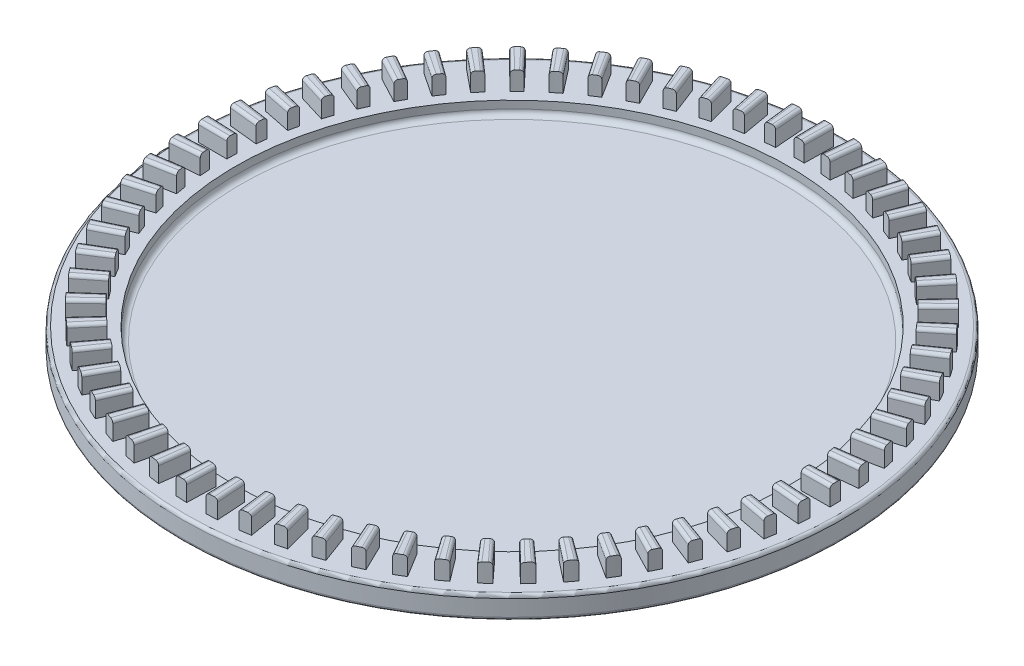
SolidWorks part; units mm, degrees
material "Copper"
ref_plane "Front Plane" through (0, 0, 0) normal (0, 0, 1) x (1, 0, 0)
ref_plane "Top Plane" through (0, 0, 0) normal (0, 1, 0) x (1, 0, 0)
ref_plane "Right Plane" through (0, 0, 0) normal (1, 0, 0) x (0, 0, -1)
sketch "Sketch3" plane through (0, 0, 0) normal (0, 0, 1) x (1, 0, 0)
  line L0 (-30.8, 1.22) -> (-26.1, 1.22)
  line L2 (-31.1, 0.92) -> (-31.1, -0.6072)
  line L3 (-25.6, 0) -> (0, 0)
  line L4 (-28.5151, -1.5) -> (0, -1.5)
  line L5 (0, -1.5) -> (0, 0)
  line L6 (-26.1, 1.22) -> (-26.1, 0.5)
  line L7 (0, 249.9038) -> (0, -246.3343) construction
  arc A0 (-30.9458, -0.8694) -> (-28.5151, -1.5) centre (-28.5151, 3.5) ccw
  arc A1 (-25.6, 0) -> (-26.1, 0.5) centre (-25.6, 0.5) cw
  arc A2 (-30.8, 1.22) -> (-31.1, 0.92) centre (-30.8, 0.92) ccw
  arc A3 (-31.1, -0.6072) -> (-30.9458, -0.8694) centre (-30.8, -0.6072) ccw
  point P14 (-31.1, 1.22)
  point P17 (-31.1, -0.78)
  dimension "D3" = 5
  dimension "D7" = 0.5
  dimension "D8" = 0.3
  dimension "D1" = 5
  dimension "D2" = 2
  dimension "D4" = 2.72
  dimension "D5" = 1.5
  dimension "D6" = 31.1
revolve "Revolve1" add sketch "Sketch3" angle 360 about L7
sketch "Sketch5" plane through (0, 1.22, 0) normal (0, 1, 0) x (1, 0, 0)
  line L0 (0, 0) -> (0, 27.1) construction
  line L1 (0.473, 27.0959) -> (0.5201, 29.7955)
  line L2 (-0.473, 27.0959) -> (-0.5201, 29.7955)
  line L3 (0, 27.1) -> (0, 869.0475) construction
  line L4 (0.473, 27.0959) -> (0, 0) construction
  line L6 (-0.473, 27.0959) -> (0, 0) construction
  circle A2 centre (0, 0) radius 29.8
  circle A3 centre (0, 0) radius 29.8
  circle A5 centre (0, 0) radius 27.1
  circle A6 centre (0, 0) radius 27.1
  arc A7 (0.473, 27.0959) -> (-0.473, 27.0959) centre (0, 0) ccw
  arc A9 (0.5201, 29.7955) -> (-0.5201, 29.7955) centre (0, 0) ccw
  dimension "D3" = 1
  dimension "D4" = 1
  dimension "D1" = 1
  dimension "D2" = 1
extrude "Boss-Extrude1" add sketch "Sketch5" along normal blind 1.75 contours A6 L1 A3 L2
fillet "Fillet1" radius 0.3 2 edges at (0.4965, 2.97, -28.4457) (-0.4965, 2.97, -28.4457)
pattern_circular "CirPattern2" count 65 over 360 about axis through (0, 0, 0) along (0, 1, 0) of "Boss-Extrude1", "Fillet1"
